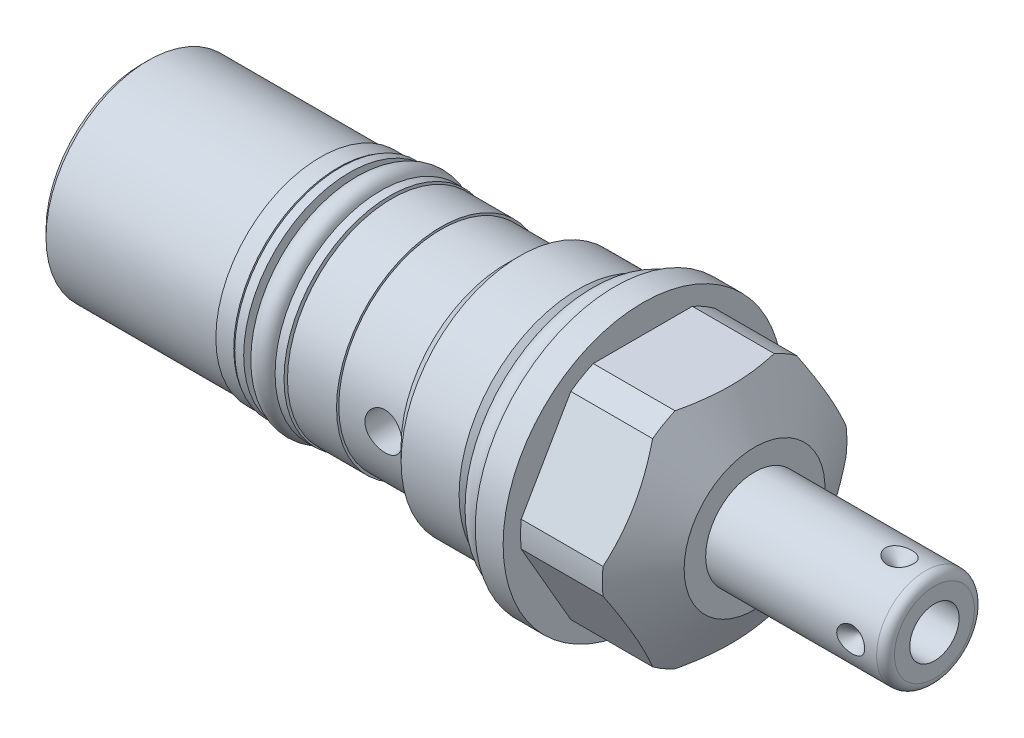
SolidWorks part; units mm, degrees
material "Alloy Steel"
ref_plane "Front Plane" through (0, 0, 0) normal (0, 0, 1) x (1, 0, 0)
ref_plane "Top Plane" through (0, 0, 0) normal (0, 1, 0) x (1, 0, 0)
ref_plane "Right Plane" through (0, 0, 0) normal (1, 0, 0) x (0, 0, -1)
ref_plane "Plane1" through (0, 0, 0) normal (1, 0, 0) x (0, 0, -1)
sketch "Sketch1" plane through (0, 0, 0) normal (1, 0, 0) x (0, 0, -1)
  circle A0 centre (0, 0) radius 15.875
  dimension "D1" = 31.75
extrude "Extrude1" add sketch "Sketch1" along normal blind 15.875 and the other way blind 53.7972
ref_plane "Plane2" through (0, 0, 0) normal (1, 0, 0) x (0, 0, -1)
sketch "Sketch2" plane through (0, 0, 0) normal (1, 0, 0) x (0, 0, -1)
  circle A0 centre (0, 0) radius 13.4937
  circle A1 centre (0, 0) radius 15.875 construction
  circle A2 centre (0, 0) radius 15.875
  dimension "D1" = 26.9875
extrude "Cut-Extrude1" cut sketch "Sketch2" against normal up to next
ref_plane "Plane3" through (0, 0, 0) normal (0, 0, 1) x (1, 0, 0)
sketch "Sketch3" plane through (0, 0, 0) normal (0, 0, 1) x (1, 0, 0)
  line L0 (11.3289, 15.875) -> (15.875, 8.001)
  line L1 (-8.1458, 0) -> (17.0188, 0) construction
  line L2 (15.875, 8.001) -> (15.875, 15.875)
  line L3 (15.875, 15.875) -> (11.3289, 15.875)
  line L4 (15.875, 15.875) -> (0, 15.875) construction
  dimension "D1" = 16.002
  dimension "D2" = 30
revolve "Cut-Revolve1" cut sketch "Sketch3" angle 360 about L1
ref_plane "Plane5" through (3.175, 0, 0) normal (-1, 0, 0) x (0, 0, 1)
sketch "Sketch5" plane through (3.175, 0, 0) normal (-1, 0, 0) x (0, 0, 1)
  line L0 (-7.3323, 12.7) -> (7.3323, 12.7)
  line L1 (7.3323, 12.7) -> (14.6647, 0)
  line L2 (14.6647, 0) -> (7.3323, -12.7)
  line L3 (7.3323, -12.7) -> (-7.3323, -12.7)
  line L4 (-7.3323, -12.7) -> (-14.6647, 0)
  line L5 (-14.6647, 0) -> (-7.3323, 12.7)
  line L6 (0, 0) -> (18.7904, 0) construction
  line L7 (0, 0) -> (7.3323, 12.7) construction
  line L8 (0, 0) -> (-7.3323, 12.7) construction
  circle A0 centre (0, 0) radius 15.875 construction
  circle A1 centre (0, 0) radius 15.875
  dimension "D1" = 25.4
  dimension "D2" = 120
  dimension "D3" = 60
extrude "Cut-Extrude3" cut sketch "Sketch5" against normal up to next
ref_plane "Plane7" through (3.175, 0, 0) normal (-1, 0, 0) x (0, 0, 1)
sketch "Sketch7" plane through (3.175, 0, 0) normal (-1, 0, 0) x (0, 0, 1)
  circle A0 centre (0, 0) radius 13.8938
  circle A1 centre (0, 0) radius 15.875 construction
  circle A2 centre (0, 0) radius 15.875
  dimension "D1" = 27.7876
extrude "Cut-Extrude5" cut sketch "Sketch7" against normal up to next
ref_plane "Plane9" through (0, 0, 0) normal (0, 0, 1) x (1, 0, 0)
sketch "Sketch9" plane through (0, 0, 0) normal (0, 0, 1) x (1, 0, 0)
  line L0 (0, 13.4937) -> (0, 12.0015)
  line L1 (0, 12.0015) -> (-2.7178, 12.0015)
  line L2 (-2.7178, 12.0015) -> (-4.21, 13.4937)
  line L3 (-4.4206, 0) -> (0.2105, 0) construction
  line L4 (0, 13.4937) -> (-4.21, 13.4937)
  line L5 (0, 13.4937) -> (-53.7972, 13.4937) construction
  line L6 (0, 15.875) -> (0, -15.875) construction
  dimension "D1" = 2.7178
  dimension "D2" = 45
  dimension "D3" = 24.003
revolve "Cut-Revolve3" cut sketch "Sketch9" angle 360 about L3
ref_plane "Plane10" through (0, 0, 0) normal (0, 0, 1) x (1, 0, 0)
sketch "Sketch10" plane through (0, 0, 0) normal (0, 0, 1) x (1, 0, 0)
  line L0 (-10.8013, 13.4937) -> (-12.4206, 11.8745)
  line L1 (-12.4206, 11.8745) -> (-53.7972, 11.8745)
  line L2 (-55.947, 0) -> (-8.6516, 0) construction
  line L3 (-2.7178, 12.0015) -> (-2.7178, -12.0015) construction
  line L4 (-53.7972, 13.4937) -> (-53.7972, 11.8745)
  line L6 (-4.21, 13.4937) -> (-53.7972, 13.4937) construction
  line L7 (-10.8013, 13.4937) -> (-53.7972, 13.4937)
  dimension "D1" = 23.749
  dimension "D2" = 45
  dimension "D3" = 9.7028
revolve "Cut-Revolve4" cut sketch "Sketch10" angle 360 about L2
ref_plane "Plane12" through (0, 0, 0) normal (0, 0, 1) x (1, 0, 0)
sketch "Sketch12" plane through (0, 0, 0) normal (0, 0, 1) x (1, 0, 0)
  line L0 (-31.4452, 11.8745) -> (-31.4452, 9.8298)
  line L1 (-31.4452, 9.8298) -> (-25.3365, 9.8298)
  line L2 (-25.3365, 9.8298) -> (-25.3365, 11.8745)
  line L3 (-31.7506, 0) -> (-25.0311, 0) construction
  line L4 (-31.4452, 11.8745) -> (-25.3365, 11.8745)
  line L5 (-12.4206, 11.8745) -> (-53.7972, 11.8745) construction
  line L6 (-53.7972, 11.8745) -> (-53.7972, -11.8745) construction
  dimension "D1" = 6.1087
  dimension "D2" = 19.6596
  dimension "D3" = 22.352
revolve "Cut-Revolve6" cut sketch "Sketch12" angle 360 about L3
ref_plane "Plane14" through (0, 0, 0) normal (0, 0, 1) x (0, -1, 0)
sketch "Sketch14" plane through (0, 0, 0) normal (0, 0, 1) x (0, -1, 0)
  line L0 (11.8745, -53.7972) -> (11.6205, -53.7972)
  line L1 (11.6205, -53.7972) -> (11.6205, -33.4772)
  line L2 (11.6205, -33.4772) -> (11.8745, -33.4772)
  line L3 (11.8745, -33.4772) -> (11.8745, -53.7972)
  line L4 (11.8745, -12.4206) -> (11.6205, -12.4206)
  line L5 (11.6205, -12.4206) -> (11.6205, -19.7612)
  line L6 (11.6205, -19.7612) -> (11.8745, -19.7612)
  line L7 (11.8745, -19.7612) -> (11.8745, -12.4206)
  line L8 (0, -55.866) -> (0, -10.3518) construction
  line L9 (11.8745, -53.7972) -> (11.8745, -31.4452) construction
  line L10 (11.8745, -25.3365) -> (11.8745, -12.4206) construction
  line L11 (-11.8745, -53.7972) -> (11.8745, -53.7972) construction
  dimension "D1" = 13.716
  dimension "D2" = 23.241
  dimension "D3" = 20.32
  dimension "D4" = 7.3406
revolve "Cut-Revolve8" cut sketch "Sketch14" angle 360 about L8
ref_plane "Plane15" through (0, 0, 0) normal (0, 0, 1) x (0, -1, 0)
sketch "Sketch15" plane through (0, 0, 0) normal (0, 0, 1) x (0, -1, 0)
  line L0 (0, -3.0937) -> (0, 0.1473) construction
  line L1 (-15.875, 0) -> (15.875, 0) construction
  circle A0 centre (13.4747, -1.4732) radius 1.4732
  dimension "D1" = 2.9464
  dimension "D2" = 1.4732
  dimension "D3" = 26.9494
revolve "Revolve1" add sketch "Sketch15" angle 360 about L0
ref_plane "Plane16" through (0, 0, 0) normal (0, 0, 1) x (0, -1, 0)
sketch "Sketch16" plane through (0, 0, 0) normal (0, 0, 1) x (0, -1, 0)
  line L0 (9.8298, -25.5905) -> (12.0142, -25.5905)
  line L1 (12.0142, -25.5905) -> (12.0142, -26.6065)
  line L2 (12.0142, -26.6065) -> (9.8298, -26.6065)
  line L3 (9.8298, -26.6065) -> (9.8298, -25.5905)
  line L4 (9.8298, -31.1912) -> (12.0142, -31.1912)
  line L5 (12.0142, -31.1912) -> (12.0142, -30.1752)
  line L6 (12.0142, -30.1752) -> (9.8298, -30.1752)
  line L7 (9.8298, -30.1752) -> (9.8298, -31.1912)
  line L8 (0, -31.4712) -> (0, -25.3105) construction
  line L9 (-11.8745, -25.3365) -> (11.8745, -25.3365) construction
  line L10 (11.8745, -31.4452) -> (-11.8745, -31.4452) construction
  dimension "D1" = 1.016
  dimension "D2" = 19.6596
  dimension "D3" = 24.0284
  dimension "D4" = 0.254
  dimension "D5" = 0.254
revolve "Revolve2" add sketch "Sketch16" angle 360 about L8
ref_plane "Plane17" through (0, 0, 0) normal (0, 0, 1) x (0, -1, 0)
sketch "Sketch17" plane through (0, 0, 0) normal (0, 0, 1) x (0, -1, 0)
  line L0 (0, -31.7506) -> (0, -25.0311) construction
  line L1 (12.0142, -30.1752) -> (-12.0142, -30.1752) construction
  circle A0 centre (11.1379, -28.3909) radius 1.3081
  point P0 (9.8298, -25.3365)
  point P1 (9.8298, -31.4452)
  dimension "D1" = 2.6162
  dimension "D2" = 22.2758
  dimension "D3" = 1.7843
revolve "Revolve3" add sketch "Sketch17" angle 360 about L0
ref_plane "Plane18" through (0, 0, 0) normal (0, 0, 1) x (0, -1, 0)
sketch "S2D0001" plane through (0, 0, 0) normal (0, 0, 1) x (0, -1, 0)
  line L0 (0, 15.875) -> (-5.5562, 15.875)
  line L1 (-5.5562, 15.875) -> (-5.5562, 35.306)
  line L2 (-4.5402, 36.322) -> (0, 36.322)
  line L3 (0, 36.322) -> (0, 15.875)
  line L4 (0, 7.2658) -> (0, 37.3443) construction
  line L5 (8.001, 15.875) -> (-8.001, 15.875) construction
  line L6 (-15.875, 0) -> (15.875, 0) construction
  arc A0 (-4.5402, 36.322) -> (-5.5562, 35.306) centre (-4.5402, 35.306) ccw
  dimension "D2" = 1.016
  dimension "D1" = 11.1125
  dimension "D3" = 36.322
revolve "Revolve4" add sketch "S2D0001" angle 360 about L4
ref_plane "Plane19" through (36.322, -2.8067, 0) normal (0, 0, 1) x (0, -1, 0)
sketch "Sketch19" plane through (36.322, -2.8067, 0) normal (0, 0, 1) x (0, -1, 0)
  line L0 (0, 0) -> (0, -10.16)
  line L1 (0, -10.16) -> (-2.8067, -11.8464)
  line L2 (0, 0) -> (-2.8067, 0)
  line L3 (-2.8067, 0) -> (-2.8067, -11.8464)
  line L4 (-2.8067, -18.6227) -> (-2.8067, 0.5923) construction
  line L5 (1.7335, 0) -> (-7.3469, 0) construction
  dimension "D1" = 5.6134
  dimension "D2" = 10.16
  dimension "D3" = 59
revolve "Cut-Revolve9" cut sketch "Sketch19" angle 360 about L4
ref_plane "Plane20" through (32.3596, 0, -5.5562) normal (0, 1, 0) x (1, 0, 0)
sketch "S2D0002" plane through (32.3596, 0, -5.5562) normal (0, 1, 0) x (1, 0, 0)
  line L0 (0, 0) -> (1.5875, 0)
  line L1 (1.5875, 0) -> (0, -1.5875)
  line L2 (0, 0) -> (0, -1.5875)
  line L3 (0, -3.3652) -> (0, 0.0794) construction
  line L4 (2.9464, 0) -> (-16.4846, 0) construction
  line L5 (3.9624, -10.0965) -> (3.9624, -1.016) construction
  dimension "D1" = 3.9624
  dimension "D2" = 45
  dimension "D3" = 3.175
revolve "Cut-Revolve10" cut sketch "S2D0002" angle 360 about L3
pattern_circular "CirPattern1" count 4 over 360 about axis through (7.2658, 0, 0) along (-1, 0, 0) of "Cut-Revolve10"
chamfer "Chamfer1" distance 0.762 angle 45 1 edges at (-53.7972, 0, 11.6205)
sketch "Sketch23" plane through (0, 0, 0) normal (0, 0, 1) x (1, 0, 0)
  line L0 (-53.7972, 10.8585) -> (-53.7972, -10.8585) construction
  circle A0 centre (-14.6812, 0) radius 2.1082
  dimension "D1" = 4.2164
  dimension "D2" = 39.116
extrude "Cut-Extrude7" cut sketch "Sketch23" along normal through all
sketch "Sketch24" plane through (0, 0, 0) normal (0, 0, 1) x (1, 0, 0)
  line L0 (0, 0) -> (-56.0091, 0) construction
  line L1 (-53.7972, 4.5783) -> (-51.7271, 4.1383)
  line L2 (-53.7972, 10.8585) -> (-53.7972, -10.8585) construction
  line L3 (-51.7271, 4.1383) -> (-51.0432, 3.4544)
  line L4 (-51.0432, 3.4544) -> (-42.0116, 3.4544)
  line L5 (-42.0116, 3.4544) -> (-42.0116, 0)
  line L6 (-42.0116, 0) -> (-53.7972, 0)
  line L7 (-53.7972, 0) -> (-53.7972, 4.5783)
  dimension "D1" = 6.9088
  dimension "D2" = 11.7856
  dimension "D3" = 45
  dimension "D4" = 12
  dimension "D5" = 9.1567
  dimension "D6" = 2.0701
revolve "Cut-Revolve11" cut sketch "Sketch24" angle 360 about L0
